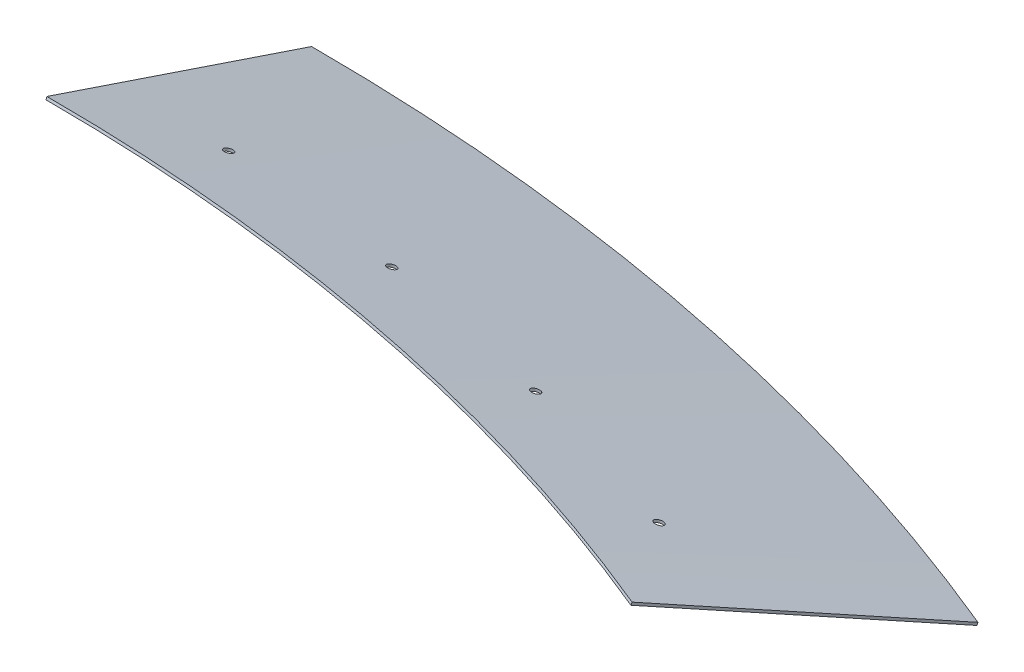
SolidWorks part; units mm, degrees
ref_plane "Front Plane" through (0, 0, 0) normal (0, 0, 1) x (1, 0, 0)
ref_plane "Top Plane" through (0, 0, 0) normal (0, 1, 0) x (1, 0, 0)
ref_plane "Right Plane" through (0, 0, 0) normal (1, 0, 0) x (0, 0, -1)
sketch "Sketch8" plane through (0, 0, 0) normal (1, 0, 0) x (0, 0, -1)
  line L3 (0, 0) -> (2162, 0) construction
  line L4 (2162, 0) -> (2162, 101) construction
  line L5 (2162, 0) -> (2462, 0) construction
  line L6 (2162, 101) -> (2462, 0)
  line L7 (2162.9572, 103.8432) -> (2462.9572, 2.8432)
  line L8 (2162, 101) -> (2162.9572, 103.8432)
  line L9 (2462, 0) -> (2462.9572, 2.8432)
  dimension "D1" = 2162
  dimension "D2" = 300
  dimension "D3" = 101
  dimension "D4" = 3
ref_axis "Axis1" through (0, 453.4871, 0) along (0, -1, 0)
revolve "Revolve1" add sketch "Sketch8" angle 22.5 about axis through (0, 453.4871, 0) along (0, -1, 0)
sketch "Sketch10" plane through (0, 0, 0) normal (0, 1, 0) x (1, 0, 0)
  line L0 (0, 0) -> (141.7777, 2458.8732) construction
  line L1 (0, 2462.9572) -> (0, 2162.9572) construction
  line L2 (421.7853, 2120.4578) -> (480.3124, 2414.6934) construction
  line L3 (480.3124, 2414.6934) -> (-36.7647, 2517.5464) construction
  arc A7 (942.5329, 2275.4758) -> (0, 2462.9572) centre (0, 0) ccw construction
  circle A8 centre (129.1485, 2239.8423) radius 5
  arc A9 (827.3616, 1997.4275) -> (0, 2162) centre (0, 0) ccw construction
  arc A10 (942.1666, 2274.5914) -> (0, 2462) centre (0, 0) ccw construction
  circle A11 centre (335.4919, 2218.3368) radius 5
  circle A12 centre (538.9666, 2177.8632) radius 5
  circle A13 centre (737.8329, 2118.7675) radius 5
  point P28 (0, 0)
  dimension "D1" = 3.3
  dimension "D2" = 10
  dimension "D3" = 240
  dimension "D4" = 4
extrude "Cut-Extrude1" cut sketch "Sketch10" along normal up to surface (78.3866 mm away)
